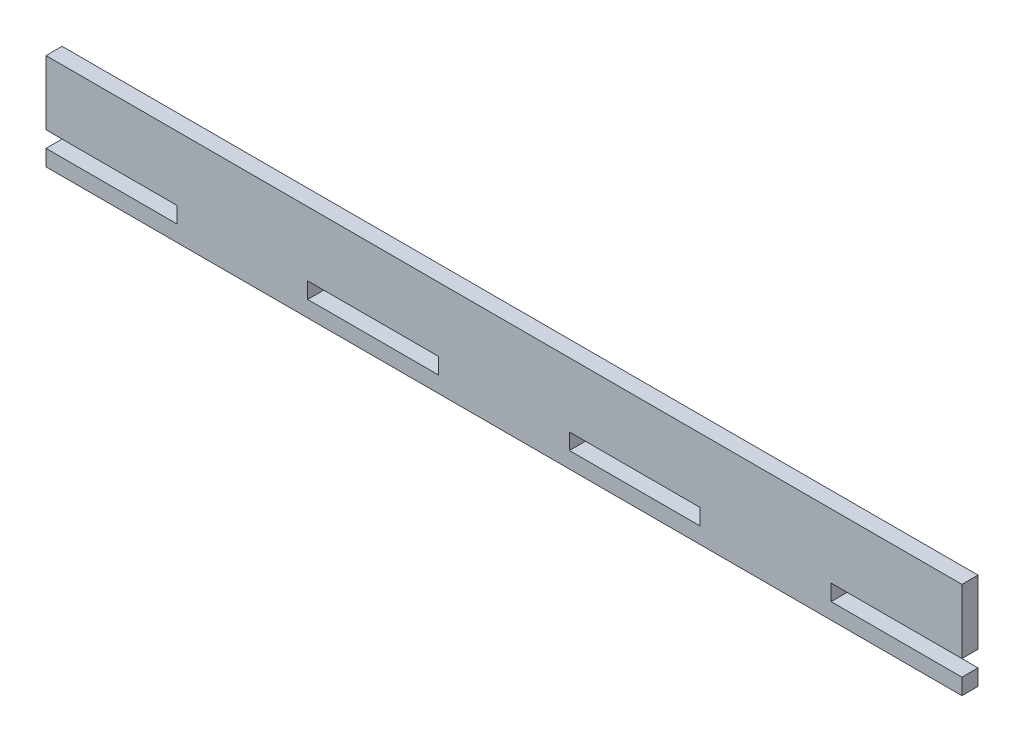
SolidWorks part; units mm, degrees
material "Contreplaqué pin"
ref_plane "Plan de face" through (0, 0, 0) normal (0, 0, 1) x (1, 0, 0)
ref_plane "Plan de dessus" through (0, 0, 0) normal (0, 1, 0) x (1, 0, 0)
ref_plane "Plan de droite" through (0, 0, 0) normal (1, 0, 0) x (0, 0, -1)
sketch "Esquisse1" plane through (0, 0, 0) normal (0, 0, 1) x (1, 0, 0)
  line L0 (0, 10) -> (0, 30)
  line L1 (0, 0) -> (285, 0)
  line L2 (0, 0) -> (0, 5)
  line L3 (0, 30) -> (285, 30)
  line L4 (285, 0) -> (285, 5)
  line L5 (0, 10) -> (40.7143, 10)
  line L7 (0, 5) -> (40.7143, 5)
  line L8 (40.7143, 10) -> (40.7143, 5)
  line L9 (81.4286, 5) -> (122.1429, 5)
  line L10 (81.4286, 5) -> (81.4286, 10)
  line L11 (81.4286, 10) -> (122.1429, 10)
  line L12 (122.1429, 5) -> (122.1429, 10)
  line L13 (244.2857, 5) -> (285, 5)
  line L14 (244.2857, 5) -> (244.2857, 10)
  line L15 (244.2857, 10) -> (285, 10)
  line L17 (162.8571, 5) -> (203.5714, 5)
  line L18 (162.8571, 5) -> (162.8571, 10)
  line L19 (162.8571, 10) -> (203.5714, 10)
  line L20 (203.5714, 5) -> (203.5714, 10)
  line L21 (285, 10) -> (285, 30)
  point P21 (67.465, 12.5438)
  point P22 (44.5342, 7.3386)
  dimension "D1" = 30
  dimension "D2" = 285
  dimension "D3" = 5
  dimension "D4" = 5
  dimension "D5" = 40.7143
  dimension "D6" = 40.7143
  dimension "D7" = 40.7143
extrude "Boss.-Extru.1" add sketch "Esquisse1" along normal blind 5
equation "\"D5@Esquisse1\"=\"D2@Esquisse1\"/7"
equation "\"D6@Esquisse1\"=\"D5@Esquisse1\""
equation "\"D7@Esquisse1\"=\"D6@Esquisse1\""
